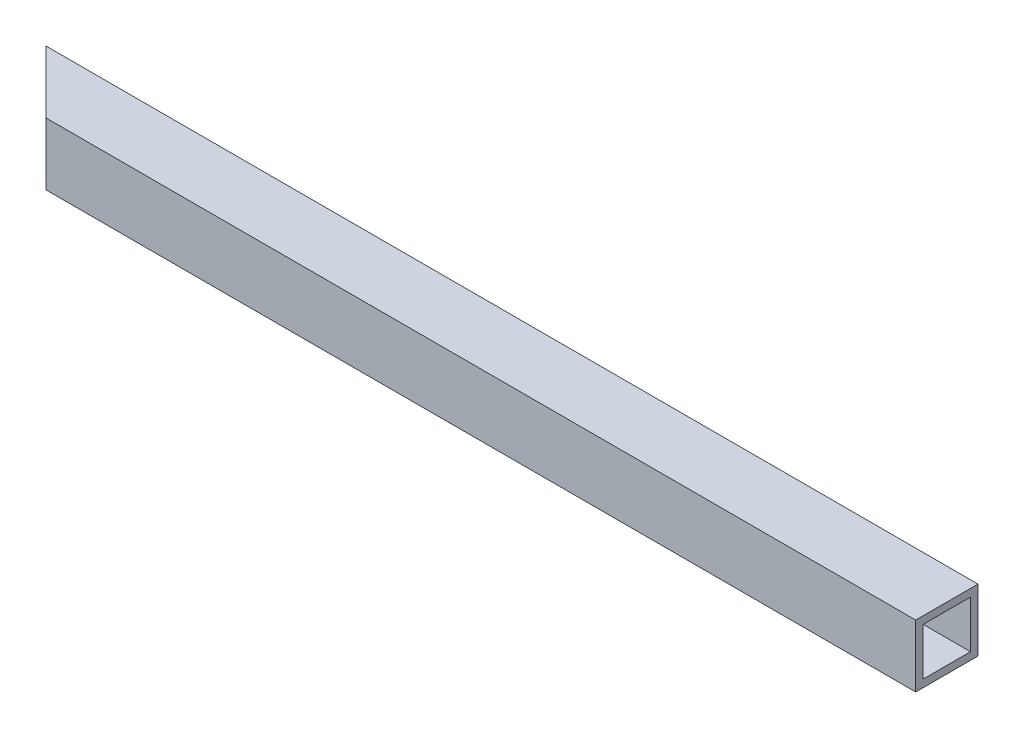
SolidWorks part; units mm, degrees
ref_plane "Front Plane" through (0, 0, 0) normal (0, 0, 1) x (1, 0, 0)
ref_plane "Top Plane" through (0, 0, 0) normal (0, 1, 0) x (1, 0, 0)
ref_plane "Right Plane" through (0, 0, 0) normal (1, 0, 0) x (0, 0, -1)
sketch "Sketch1" plane through (0, 0, 0) normal (0, 1, 0) x (1, 0, 0)
  line L1 (-174.5, 170.5609) -> (174.5, 170.5609)
  line L8 (-199.5, 195.5609) -> (174.5, 195.5609)
  line L9 (174.5, 170.5609) -> (174.5, 195.5609)
  line L11 (-174.5, 170.5609) -> (-199.5, 195.5609)
  line L12 (199.5, 195.5609) -> (199.5, -203.4391) construction
  line L13 (-199.5, 195.5609) -> (-199.5, -203.4391) construction
  line L14 (-174.5, 170.5609) -> (-174.5, -178.4391) construction
  line L15 (-174.5, -178.4391) -> (174.5, -178.4391) construction
  line L16 (-199.5, -203.4391) -> (199.5, -203.4391) construction
  line L17 (174.5, 170.5609) -> (174.5, -178.4391) construction
  line L18 (-199.5, 195.5609) -> (199.5, 195.5609) construction
  dimension "D1" = 25
extrude "Boss-Extrude1" add sketch "Sketch1" along normal blind 25
shell "Shell1" thickness 3
